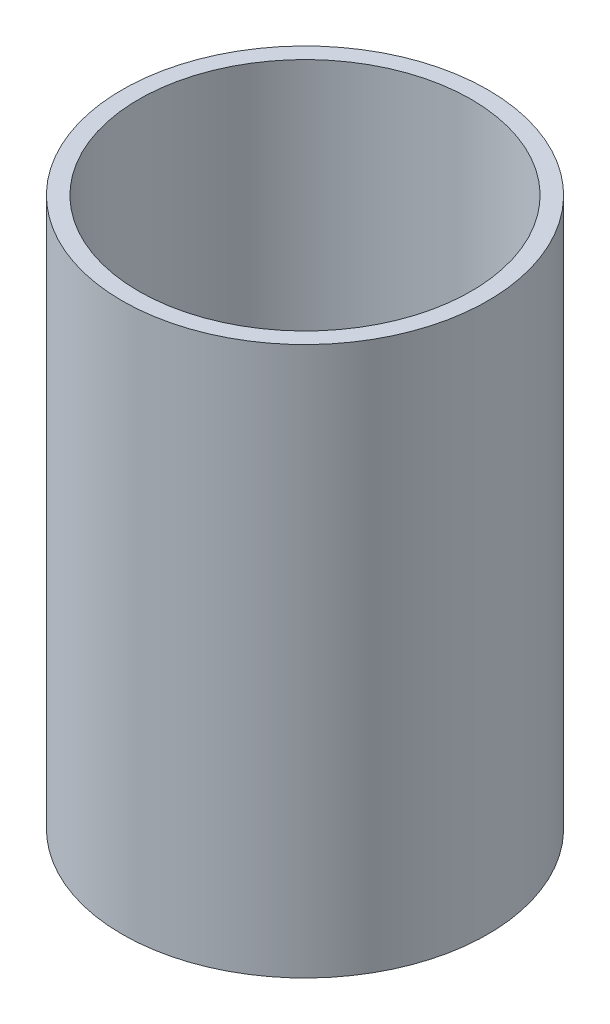
SolidWorks part; units mm, degrees
ref_plane "Front" through (0, 0, 0) normal (0, 0, 1) x (1, 0, 0)
ref_plane "Top" through (0, 0, 0) normal (0, 1, 0) x (1, 0, 0)
ref_plane "Right" through (0, 0, 0) normal (1, 0, 0) x (0, 0, -1)
sketch "Sketch1" plane through (0, 0, 0) normal (0, 1, 0) x (1, 0, 0)
  circle A0 centre (0, 0) radius 11
  circle A1 centre (0, 0) radius 10
  dimension "D1" = 20
  dimension "D2" = 22
extrude "Boss-Extrude1" add sketch "Sketch1" along normal blind 33
